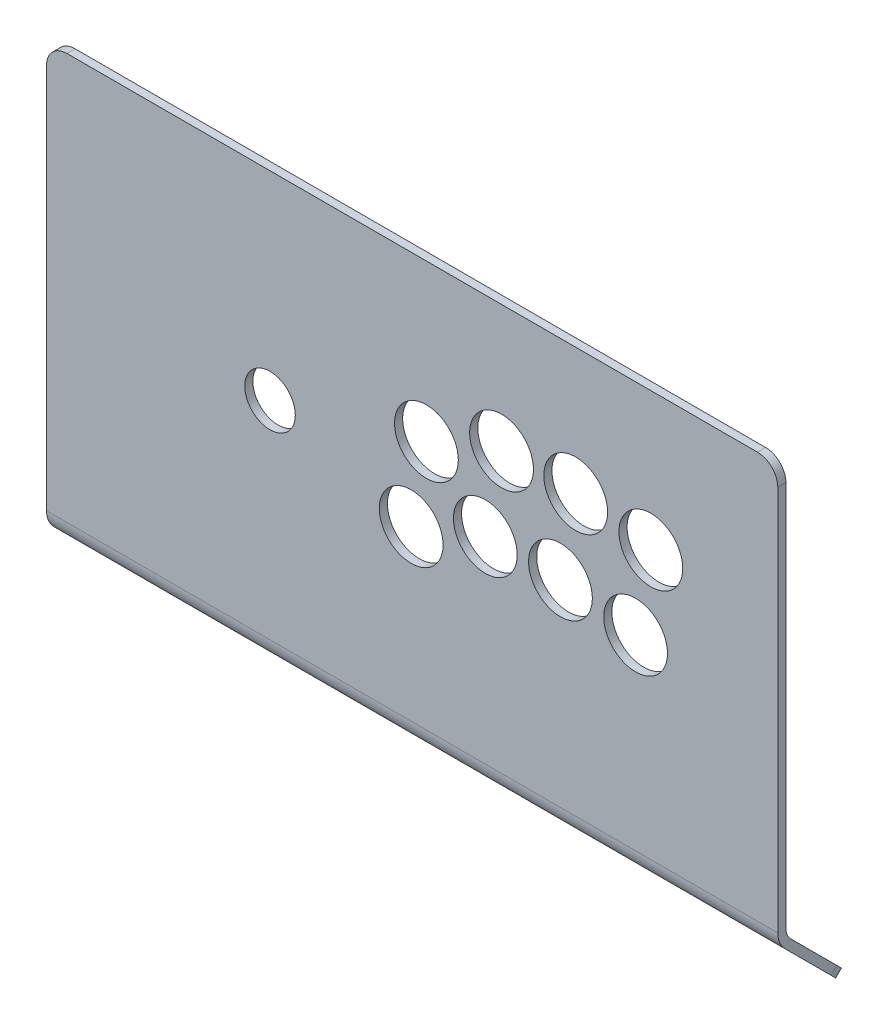
SolidWorks part; units mm, degrees
ref_plane "Alzado" through (0, 0, 0) normal (0, 0, 1) x (1, 0, 0)
ref_plane "Planta" through (0, 0, 0) normal (0, 1, 0) x (1, 0, 0)
ref_plane "Vista lateral" through (0, 0, 0) normal (1, 0, 0) x (0, 0, -1)
sketch "Model" plane through (0, 0, 0) normal (0, 0, 1) x (1, 0, 0)
  line L0 (0, 125) -> (0, -125) construction
  line L1 (-180, 125) -> (180, 125)
  line L2 (-180, 125) -> (-180, -125)
  line L3 (-180, -125) -> (180, -125)
  line L4 (-180, -75) -> (180, -75) construction
  line L5 (180, 125) -> (180, -125)
  spline S0 degree 3 poles (-56.8187, 26.8821) (-56.8187, 33.7469) (-62.3836, 39.3114) (-69.2483, 39.3114) knots 0 0 0 0 1 1 1 1
  spline S1 degree 3 poles (-69.2483, 39.3114) (-76.1131, 39.3114) (-81.6783, 33.7469) (-81.6783, 26.8821) knots 1 1 1 1 2 2 2 2
  spline S2 degree 3 poles (-81.6783, 26.8821) (-81.6783, 20.0173) (-76.1131, 14.4528) (-69.2483, 14.4528) knots 2 2 2 2 3 3 3 3
  spline S3 degree 3 poles (-69.2483, 14.4528) (-62.3836, 14.4528) (-56.8187, 20.0173) (-56.8187, 26.8821) knots 3 3 3 3 4 4 4 4
  spline S4 degree 3 poles (59.4626, 62.4254) (59.4626, 71.1026) (52.4291, 78.1364) (43.7516, 78.1364) knots 0 0 0 0 1 1 1 1
  spline S5 degree 3 poles (43.7516, 78.1364) (35.0748, 78.1364) (28.0402, 71.1026) (28.0402, 62.4254) knots 1 1 1 1 2 2 2 2
  spline S6 degree 3 poles (28.0402, 62.4254) (28.0402, 53.7483) (35.0748, 46.7144) (43.7516, 46.7144) knots 2 2 2 2 3 3 3 3
  spline S7 degree 3 poles (43.7516, 46.7144) (52.4291, 46.7144) (59.4626, 53.7483) (59.4626, 62.4254) knots 3 3 3 3 4 4 4 4
  spline S8 degree 3 poles (96.199, 62.4254) (96.199, 71.1026) (89.1651, 78.1364) (80.488, 78.1364) knots 0 0 0 0 1 1 1 1
  spline S9 degree 3 poles (80.488, 78.1364) (71.8115, 78.1364) (64.7772, 71.1026) (64.7772, 62.4254) knots 1 1 1 1 2 2 2 2
  spline S10 degree 3 poles (64.7772, 62.4254) (64.7772, 53.7483) (71.8115, 46.7144) (80.488, 46.7144) knots 2 2 2 2 3 3 3 3
  spline S11 degree 3 poles (80.488, 46.7144) (89.1651, 46.7144) (96.199, 53.7483) (96.199, 62.4254) knots 3 3 3 3 4 4 4 4
  spline S12 degree 3 poles (133.1329, 56.9314) (133.1329, 65.6086) (126.099, 72.6424) (117.4219, 72.6424) knots 0 0 0 0 1 1 1 1
  spline S13 degree 3 poles (117.4219, 72.6424) (108.7447, 72.6424) (101.7108, 65.6086) (101.7108, 56.9314) knots 1 1 1 1 2 2 2 2
  spline S14 degree 3 poles (101.7108, 56.9314) (101.7108, 48.2542) (108.7447, 41.2203) (117.4219, 41.2203) knots 2 2 2 2 3 3 3 3
  spline S15 degree 3 poles (117.4219, 41.2203) (126.099, 41.2203) (133.1329, 48.2542) (133.1329, 56.9314) knots 3 3 3 3 4 4 4 4
  spline S16 degree 3 poles (125.465, 16.7739) (125.465, 25.4518) (118.4311, 32.4857) (109.754, 32.4857) knots 0 0 0 0 1 1 1 1
  spline S17 degree 3 poles (109.754, 32.4857) (101.0768, 32.4857) (94.0429, 25.4518) (94.0429, 16.7739) knots 1 1 1 1 2 2 2 2
  spline S18 degree 3 poles (94.0429, 16.7739) (94.0429, 8.0974) (101.0768, 1.0636) (109.754, 1.0636) knots 2 2 2 2 3 3 3 3
  spline S19 degree 3 poles (109.754, 1.0636) (118.4311, 1.0636) (125.465, 8.0974) (125.465, 16.7739) knots 3 3 3 3 4 4 4 4
  spline S20 degree 3 poles (88.5324, 22.2693) (88.5324, 30.9465) (81.4982, 37.9803) (72.8214, 37.9803) knots 0 0 0 0 1 1 1 1
  spline S21 degree 3 poles (72.8214, 37.9803) (64.1439, 37.9803) (57.11, 30.9465) (57.11, 22.2693) knots 1 1 1 1 2 2 2 2
  spline S22 degree 3 poles (57.11, 22.2693) (57.11, 13.5922) (64.1439, 6.5583) (72.8214, 6.5583) knots 2 2 2 2 3 3 3 3
  spline S23 degree 3 poles (72.8214, 6.5583) (81.4982, 6.5583) (88.5324, 13.5922) (88.5324, 22.2693) knots 3 3 3 3 4 4 4 4
  spline S24 degree 3 poles (51.7947, 22.2693) (51.7947, 30.9465) (44.7612, 37.9803) (36.0837, 37.9803) knots 0 0 0 0 1 1 1 1
  spline S25 degree 3 poles (36.0837, 37.9803) (27.4068, 37.9803) (20.3723, 30.9465) (20.3723, 22.2693) knots 1 1 1 1 2 2 2 2
  spline S26 degree 3 poles (20.3723, 22.2693) (20.3723, 13.5922) (27.4068, 6.5583) (36.0837, 6.5583) knots 2 2 2 2 3 3 3 3
  spline S27 degree 3 poles (36.0837, 6.5583) (44.7612, 6.5583) (51.7947, 13.5922) (51.7947, 22.2693) knots 3 3 3 3 4 4 4 4
  spline S28 degree 3 poles (15.1939, 7.9564) (15.1939, 16.6336) (8.16, 23.6675) (-0.5165, 23.6675) knots 0 0 0 0 1 1 1 1
  spline S29 degree 3 poles (-0.5165, 23.6675) (-9.1943, 23.6675) (-16.2282, 16.6336) (-16.2282, 7.9564) knots 1 1 1 1 2 2 2 2
  spline S30 degree 3 poles (-16.2282, 7.9564) (-16.2282, -0.7201) (-9.1943, -7.7539) (-0.5165, -7.7539) knots 2 2 2 2 3 3 3 3
  spline S31 degree 3 poles (-0.5165, -7.7539) (8.16, -7.7539) (15.1939, -0.7201) (15.1939, 7.9564) knots 3 3 3 3 4 4 4 4
  spline S32 degree 3 poles (22.4455, 48.1132) (22.4455, 56.7897) (15.412, 63.8242) (6.7352, 63.8242) knots 0 0 0 0 1 1 1 1
  spline S33 degree 3 poles (6.7352, 63.8242) (-1.942, 63.8242) (-8.9762, 56.7897) (-8.9762, 48.1132) knots 1 1 1 1 2 2 2 2
  spline S34 degree 3 poles (-8.9762, 48.1132) (-8.9762, 39.436) (-1.942, 32.4021) (6.7352, 32.4021) knots 2 2 2 2 3 3 3 3
  spline S35 degree 3 poles (6.7352, 32.4021) (15.412, 32.4021) (22.4455, 39.436) (22.4455, 48.1132) knots 3 3 3 3 4 4 4 4
  dimension "D1" = 360
  dimension "D2" = 250
sketch "Croquis1" plane through (0, 0, 0) normal (1, 0, 0) x (0, 0, -1)
  line L0 (0, 0) -> (0, -200) construction
  line L9 (-2, 0) -> (-2, -200)
  line L10 (0, -200) -> (-10, -200) construction
  line L11 (0, -200) -> (10, -200) construction
  line L12 (10, -200) -> (10, -210) construction
  line L13 (10, -200) -> (50.251, -240.251) construction
  line L14 (2.9289, -207.0711) -> (32.7307, -236.8728) construction
  line L15 (10, -200) -> (2.9289, -207.0711) construction
  line L16 (1.5147, -208.4853) -> (31.3164, -238.287)
  line L17 (2, 0) -> (2, -200)
  line L18 (4.3431, -205.6569) -> (34.1449, -235.4586)
  line L19 (-2, 0) -> (2, 0)
  line L20 (31.3164, -238.287) -> (34.1449, -235.4586)
  arc A0 (0, -200) -> (2.9289, -207.0711) centre (10, -200) ccw construction
  arc A2 (-2, -200) -> (1.5147, -208.4853) centre (10, -200) ccw
  arc A3 (2, -200) -> (4.3431, -205.6569) centre (10, -200) ccw
  dimension "D1" = 45
  dimension "D2" = 45
extrude "Saliente-Extruir1" add sketch "Croquis1" along normal mid plane 360
sketch "Croquis3" plane through (0, 0, 2) normal (0, 0, 1) x (1, 0, 0)
  line L0 (0, 0) -> (0, -250) construction
  line L1 (-180, 0) -> (180, 0) construction
  line L2 (-180, 0) -> (-180, -250) construction
  line L3 (-180, -250) -> (180, -250) construction
  line L4 (-180, -200) -> (180, -200) construction
  line L5 (180, 0) -> (180, -250) construction
  line L6 (-70, -98) -> (-180, -98) construction
  line L7 (-70, -98) -> (-70, 0) construction
  circle A0 centre (-70, -98) radius 12.4506
  circle A1 centre (7, -77) radius 15.7
  circle A2 centre (-0.5, -117) radius 15.7
  circle A3 centre (36, -103) radius 15.7
  circle A4 centre (73, -103) radius 15.7
  circle A5 centre (110, -108) radius 15.7
  circle A6 centre (117.5, -68) radius 15.7
  circle A7 centre (80.5, -62.5) radius 15.7
  circle A8 centre (44, -62.5) radius 15.7
  point P1 (180, -125)
  dimension "D2" = 98
  dimension "D1" = 250
  dimension "D3" = 110
  dimension "D4" = 77
  dimension "D5" = 62.5
  dimension "D6" = 62.5
  dimension "D7" = 68
  dimension "D8" = 360
  dimension "D9" = 200
  dimension "D10" = 83
  dimension "D11" = 97
  dimension "D12" = 97
  dimension "D13" = 92
  dimension "D14" = 173
  dimension "D15" = 136
  dimension "D16" = 99.5
  dimension "D17" = 62.5
  dimension "D18" = 180.5
  dimension "D19" = 144
  dimension "D20" = 107
  dimension "D21" = 70
extrude "Cortar-Extruir1" cut sketch "Croquis3" against normal through all
fillet "Redondeo1" radius 10 4 edges at (180, 0, 0) (-180, 0, 0) (180, -236.8728, -32.7307) (-180, -236.8728, -32.7307)
